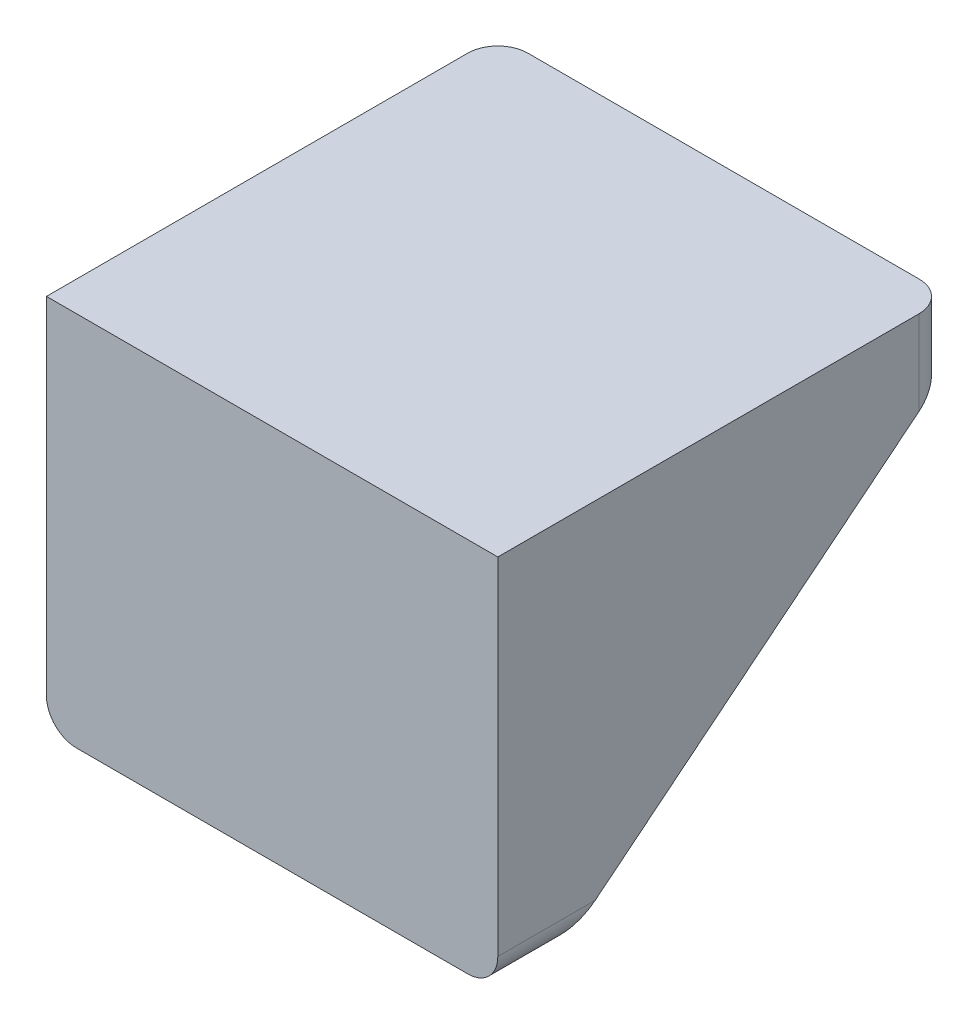
SolidWorks part; units mm, degrees
ref_plane "Front Plane" through (0, 0, 0) normal (0, 0, 1) x (1, 0, 0)
ref_plane "Top Plane" through (0, 0, 0) normal (0, 1, 0) x (1, 0, 0)
ref_plane "Right Plane" through (0, 0, 0) normal (1, 0, 0) x (0, 0, -1)
sketch "Sketch1" plane through (0, 0, 0) normal (1, 0, 0) x (0, 0, -1)
  line L0 (0, -12.5) -> (0, 12.5)
  line L1 (0, 12.5) -> (30, 12.5)
  line L2 (4, -12.5) -> (4, 8.5)
  line L3 (4, 8.5) -> (30, 8.5)
  line L4 (0, -12.5) -> (4, -12.5)
  line L5 (30, 12.5) -> (30, 8.5)
  point P4 (0, 0)
  dimension "D1" = 25
  dimension "D2" = 30
  dimension "D3" = 4
extrude "Boss-Extrude1" add sketch "Sketch1" along normal mid plane 30
sketch "Sketch2" plane through (15, 0, 0) normal (1, 0, 0) x (0, 0, -1)
  line L0 (30, 8.5) -> (4, -12.5)
  line L1 (4, -12.5) -> (4, 8.5) construction
  line L2 (4, 8.5) -> (30, 8.5) construction
  line L3 (4, -12.5) -> (4, 8.5)
  line L4 (4, 8.5) -> (30, 8.5)
extrude "Boss-Extrude2" add sketch "Sketch2" against normal blind 4
mirror "Mirror1" about plane through (0, 0, 0) normal (1, 0, 0) of "Boss-Extrude2"
fillet "Fillet1" radius 2 4 edges at (-15, 10.5, -30) (15, 10.5, -30) (15, -12.5, -2) (-15, -12.5, -2)
